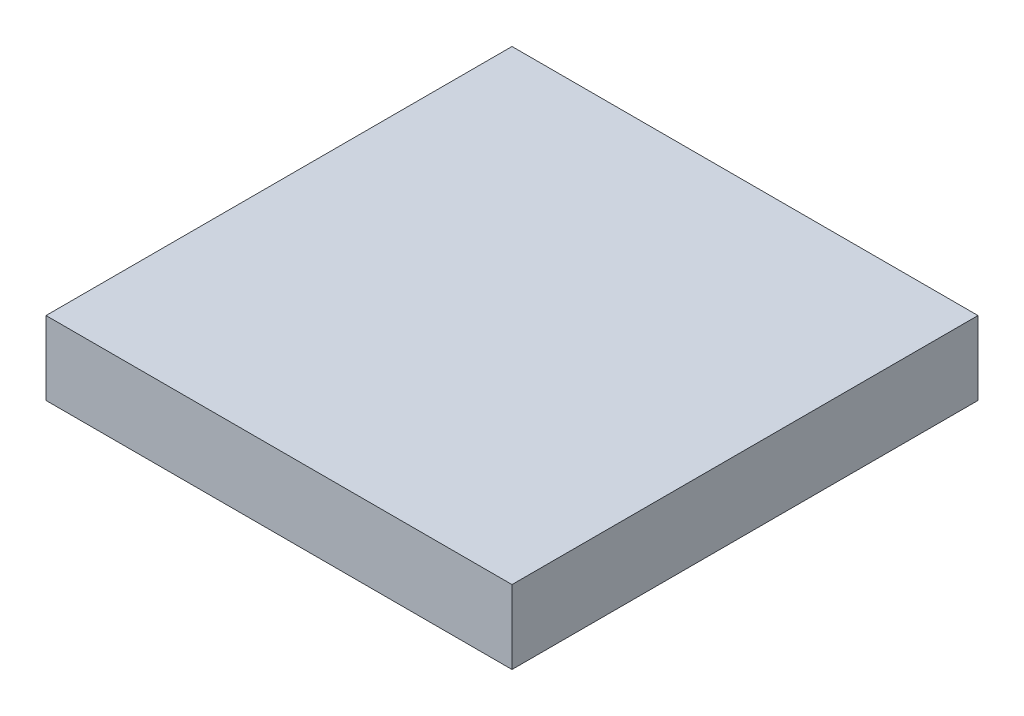
SolidWorks part; units mm, degrees
ref_plane "Front Plane" through (0, 0, 0) normal (0, 0, 1) x (1, 0, 0)
ref_plane "Top Plane" through (0, 0, 0) normal (0, 1, 0) x (1, 0, 0)
ref_plane "Right Plane" through (0, 0, 0) normal (1, 0, 0) x (0, 0, -1)
sketch "Sketch1" plane through (0, 0, 0) normal (0, 1, 0) x (1, 0, 0)
  line L1 (-45, -47.5) -> (45, -47.5)
  line L2 (-45, -47.5) -> (-45, 47.5)
  line L3 (-45, 47.5) -> (45, 47.5)
  line L4 (45, -47.5) -> (45, 47.5)
  line L5 (-45, -47.5) -> (45, 47.5) construction
  line L6 (-45, 47.5) -> (45, -47.5) construction
  point P0 (0, 0)
  dimension "D1" = 95
  dimension "D2" = 90
extrude "Boss-Extrude3" add sketch "Sketch1" along normal blind 15
sketch "Sketch5" plane through (45, 0, 0) normal (1, 0, 0) x (0, 0, -1)
  line L0 (-47.5, 0) -> (47.5, 0) construction
  line L1 (-6.6, 2) -> (8.4, 2)
  line L2 (-6.6, 2) -> (-6.6, 10.4)
  line L3 (-6.6, 10.4) -> (8.4, 10.4)
  line L4 (8.4, 2) -> (8.4, 10.4)
  dimension "D1" = 15
  dimension "D2" = 8.4
  dimension "D3" = 2
extrude "Cut-Extrude3" cut sketch "Sketch5" against normal blind 40
sketch "Sketch7" plane through (45, 0, 0) normal (1, 0, 0) x (0, 0, -1)
  line L1 (-47.5, 0) -> (47.5, 0)
  line L2 (-47.5, 0) -> (-47.5, 15)
  line L3 (-47.5, 15) -> (47.5, 15)
  line L4 (47.5, 0) -> (47.5, 15)
extrude "Boss-Extrude4" add sketch "Sketch7" along normal blind 5
sketch "Sketch8" plane through (0, 0, 47.5) normal (0, 0, 1) x (1, 0, 0)
  line L0 (-45, 15) -> (50, 15) construction
  line L1 (50, 0) -> (35, 0)
  line L2 (50, 0) -> (50, 15)
  line L3 (50, 15) -> (35, 15)
  line L4 (35, 0) -> (35, 15)
  dimension "D1" = 15
